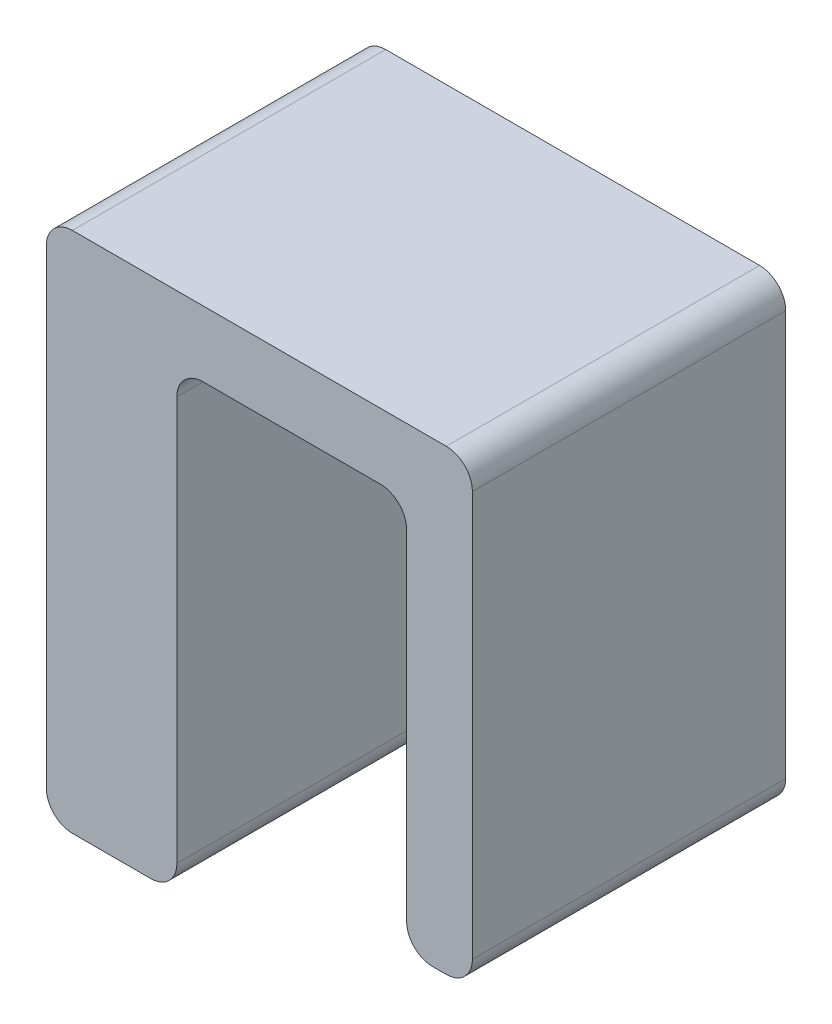
SolidWorks part; units mm, degrees
ref_plane "Front Plane" through (0, 0, 0) normal (0, 0, 1) x (1, 0, 0)
ref_plane "Top Plane" through (0, 0, 0) normal (0, 1, 0) x (1, 0, 0)
ref_plane "Right Plane" through (0, 0, 0) normal (1, 0, 0) x (0, 0, -1)
sketch "Sketch1" plane through (0, 0, 0) normal (0, 0, 1) x (1, 0, 0)
  line L0 (0, 0) -> (0, 12.7)
  line L1 (0, 12.7) -> (10.363, 12.7)
  line L2 (10.363, 12.7) -> (10.363, 1.575)
  line L3 (10.363, 1.575) -> (8.763, 1.575)
  line L4 (8.763, 1.575) -> (8.763, 11.1)
  line L5 (8.763, 11.1) -> (3.175, 11.1)
  line L6 (3.175, 11.1) -> (3.175, 0)
  line L7 (3.175, 0) -> (0, 0)
  dimension "D1" = 5.588
  dimension "D2" = 1.6
  dimension "D3" = 3.175
  dimension "D4" = 12.7
  dimension "D5" = 9.525
  dimension "D6" = 1.6
extrude "Boss-Extrude1" add sketch "Sketch1" along normal blind 7.62
fillet "Fillet1" radius 0.635 8 edges at (8.763, 11.1, 3.81) (3.175, 11.1, 3.81) (3.175, 0, 3.81) (0, 0, 3.81) (8.763, 1.575, 3.81) (10.363, 1.575, 3.81) (0, 12.7, 3.81) (10.363, 12.7, 3.81)
